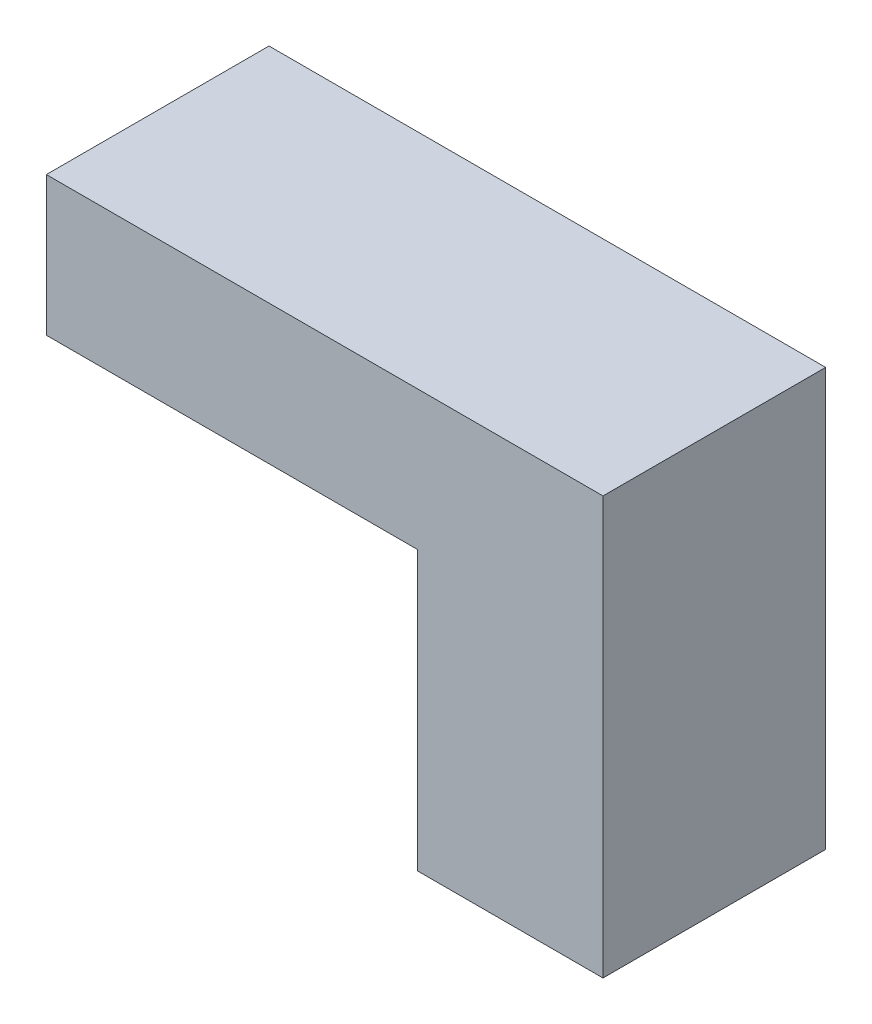
SolidWorks part; units mm, degrees
ref_plane "Front Plane" through (0, 0, 0) normal (0, 0, 1) x (1, 0, 0)
ref_plane "Top Plane" through (0, 0, 0) normal (0, 1, 0) x (1, 0, 0)
ref_plane "Right Plane" through (0, 0, 0) normal (1, 0, 0) x (0, 0, -1)
sketch "Sketch2" plane through (0, 0, 0) normal (0, 0, 1) x (1, 0, 0)
  line L0 (0, 0) -> (15.24, 0)
  line L1 (15.24, 0) -> (15.24, -11.43)
  line L2 (15.24, -11.43) -> (10.16, -11.43)
  line L3 (10.16, -11.43) -> (10.16, -3.81)
  line L4 (10.16, -3.81) -> (0, -3.81)
  line L5 (0, -3.81) -> (0, 0)
  dimension "D1" = 15.24
  dimension "D2" = 11.43
  dimension "D3" = 3.81
  dimension "D4" = 5.08
extrude "Boss-Extrude1" add sketch "Sketch2" along normal blind 6.096
